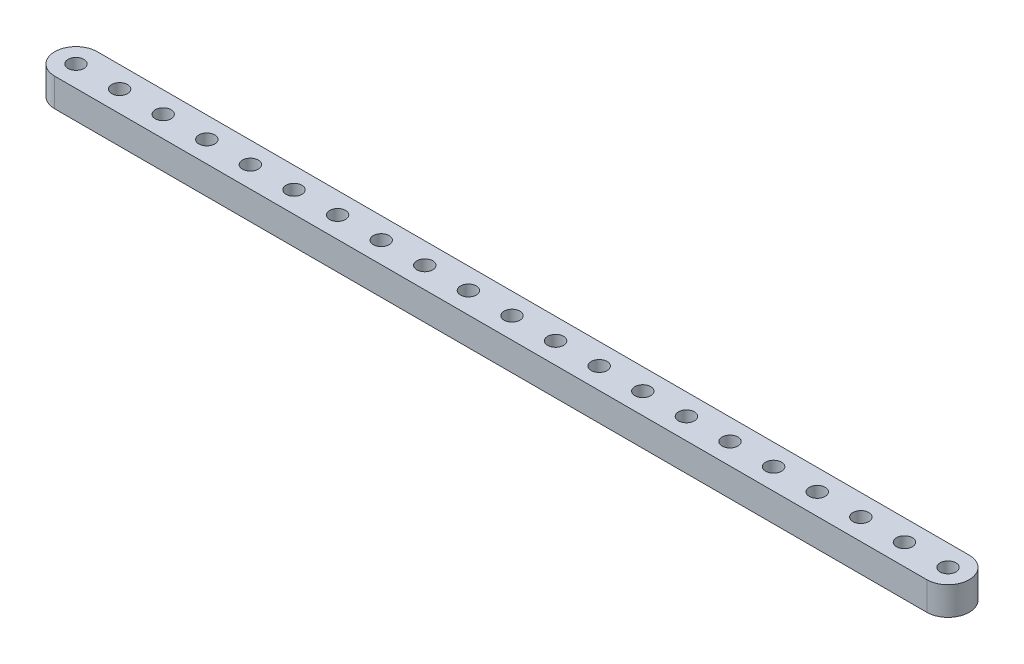
SolidWorks part; units mm, degrees
ref_plane "Front Plane" through (0, 0, 0) normal (0, 0, 1) x (1, 0, 0)
ref_plane "Top Plane" through (0, 0, 0) normal (0, 1, 0) x (1, 0, 0)
ref_plane "Right Plane" through (0, 0, 0) normal (1, 0, 0) x (0, 0, -1)
ref_plane "Plane1" through (0, 6.35, 0) normal (0, 1, 0) x (1, 0, 0)
sketch "Sketch1" plane through (0, 6.35, 0) normal (0, 1, 0) x (1, 0, 0)
  line L0 (97.79, 4.7625) -> (-97.79, 4.7625)
  line L1 (-97.79, -4.7625) -> (97.79, -4.7625)
  arc A0 (97.79, -4.7625) -> (97.79, 4.7625) centre (97.79, 0) ccw
  arc A1 (-97.79, 4.7625) -> (-97.79, -4.7625) centre (-97.79, 0) ccw
  circle A2 centre (97.79, 0) radius 1.778
  circle A3 centre (88.011, 0) radius 1.778
  circle A4 centre (78.232, 0) radius 1.778
  circle A5 centre (68.453, 0) radius 1.778
  circle A6 centre (58.674, 0) radius 1.778
  circle A7 centre (48.895, 0) radius 1.778
  circle A8 centre (39.116, 0) radius 1.778
  circle A9 centre (29.337, 0) radius 1.778
  circle A10 centre (19.558, 0) radius 1.778
  circle A11 centre (9.779, 0) radius 1.778
  circle A12 centre (0, 0) radius 1.778
  circle A13 centre (-9.779, 0) radius 1.778
  circle A14 centre (-19.558, 0) radius 1.778
  circle A15 centre (-29.337, 0) radius 1.778
  circle A16 centre (-39.116, 0) radius 1.778
  circle A17 centre (-48.895, 0) radius 1.778
  circle A18 centre (-58.674, 0) radius 1.778
  circle A19 centre (-68.453, 0) radius 1.778
  circle A20 centre (-78.232, 0) radius 1.778
  circle A21 centre (-88.011, 0) radius 1.778
  circle A22 centre (-97.79, 0) radius 1.778
extrude "Boss-Extrude1" add sketch "Sketch1" against normal blind 6.35
